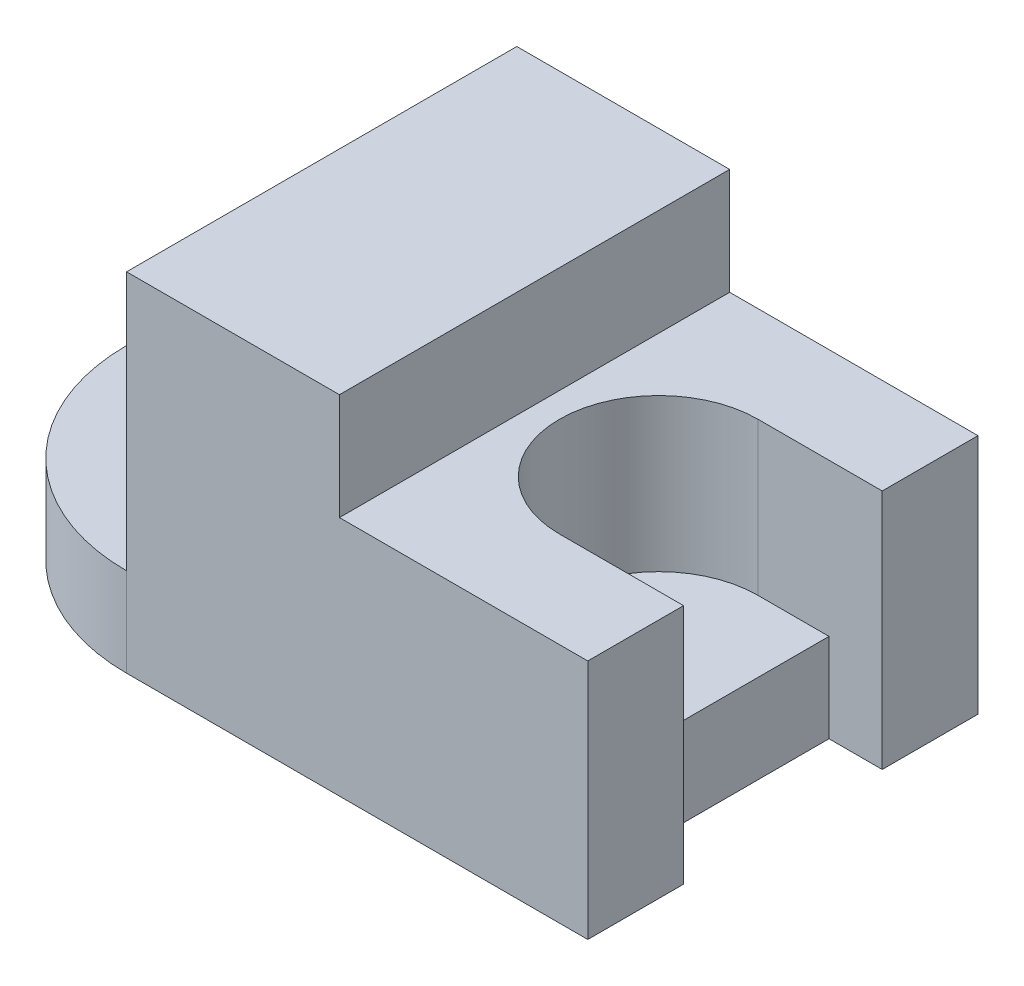
SolidWorks part; units mm, degrees
ref_plane "Front Plane" through (0, 0, 0) normal (0, 0, 1) x (1, 0, 0)
ref_plane "Top Plane" through (0, 0, 0) normal (0, 1, 0) x (1, 0, 0)
ref_plane "Right Plane" through (0, 0, 0) normal (1, 0, 0) x (0, 0, -1)
sketch "Sketch1" plane through (0, 0, 0) normal (0, 1, 0) x (1, 0, 0)
  line L0 (0, 55) -> (0, -55) construction
  line L2 (0, 55) -> (130, 55)
  line L4 (0, -55) -> (130, -55)
  line L5 (130, 55) -> (130, -55)
  circle A0 centre (0, 0) radius 15
  arc A1 (0, 55) -> (0, -55) centre (0, 0) ccw
  dimension "D1" = 30
  dimension "D2" = 110
  dimension "D3" = 130
extrude "Boss-Extrude1" add sketch "Sketch1" along normal blind 25
sketch "Sketch3" plane through (0, 25, 0) normal (0, 1, 0) x (1, 0, 0)
  line L1 (0, 55) -> (130, 55)
  line L2 (0, 55) -> (0, -55)
  line L3 (0, -55) -> (130, -55)
  line L4 (130, 55) -> (130, -55)
extrude "Boss-Extrude2" add sketch "Sketch3" along normal blind 43
sketch "Sketch4" plane through (0, 68, 0) normal (0, 1, 0) x (1, 0, 0)
  line L0 (0, -55) -> (130, -55) construction
  line L1 (0, 55) -> (60, 55)
  line L2 (0, 55) -> (0, -55)
  line L3 (0, -55) -> (60, -55)
  line L4 (60, 55) -> (60, -55)
  line L5 (130, -55) -> (130, 55) construction
  dimension "D1" = 70
extrude "Boss-Extrude3" add sketch "Sketch4" along normal blind 30
sketch "Sketch5" plane through (0, 0, 0) normal (-1, 0, 0) x (0, 0, 1)
  line L0 (0, 0) -> (0, 92.8218) construction
  line L1 (-15, 25) -> (15, 25) construction
  line L3 (0, 25) -> (-42, 25)
  line L4 (0, 25) -> (0, 53)
  line L5 (0, 53) -> (-42, 53)
  line L6 (-42, 25) -> (-42, 53)
  dimension "D1" = 28
  dimension "D2" = 42
revolve "Cut-Revolve1" cut sketch "Sketch5" angle 180 about L0
sketch "Sketch6" plane through (130, 0, 0) normal (1, 0, 0) x (0, 0, -1)
  line L0 (0, 0) -> (0, 68) construction
  line L1 (-55, 0) -> (55, 0) construction
  line L2 (-55, 68) -> (55, 68) construction
  line L3 (-55, 68) -> (55, 68) construction
  line L4 (-28, 0) -> (28, 0)
  line L5 (-28, 0) -> (-28, 68)
  line L6 (-28, 68) -> (28, 68)
  line L7 (28, 0) -> (28, 68)
  dimension "D1" = 56
extrude "Cut-Extrude1" cut sketch "Sketch6" against normal blind 15
sketch "Sketch7" plane through (0, 68, 0) normal (0, 1, 0) x (1, 0, 0)
  line L0 (130, -55) -> (130, -28) construction
  line L1 (115, 28) -> (95, 28)
  line L2 (115, 28) -> (115, -28)
  line L3 (115, -28) -> (95, -28)
  arc A0 (95, -28) -> (95, 28) centre (95, 0) cw
  dimension "D2" = 28
  dimension "D1" = 35
extrude "Cut-Extrude2" cut sketch "Sketch7" against normal blind 43
